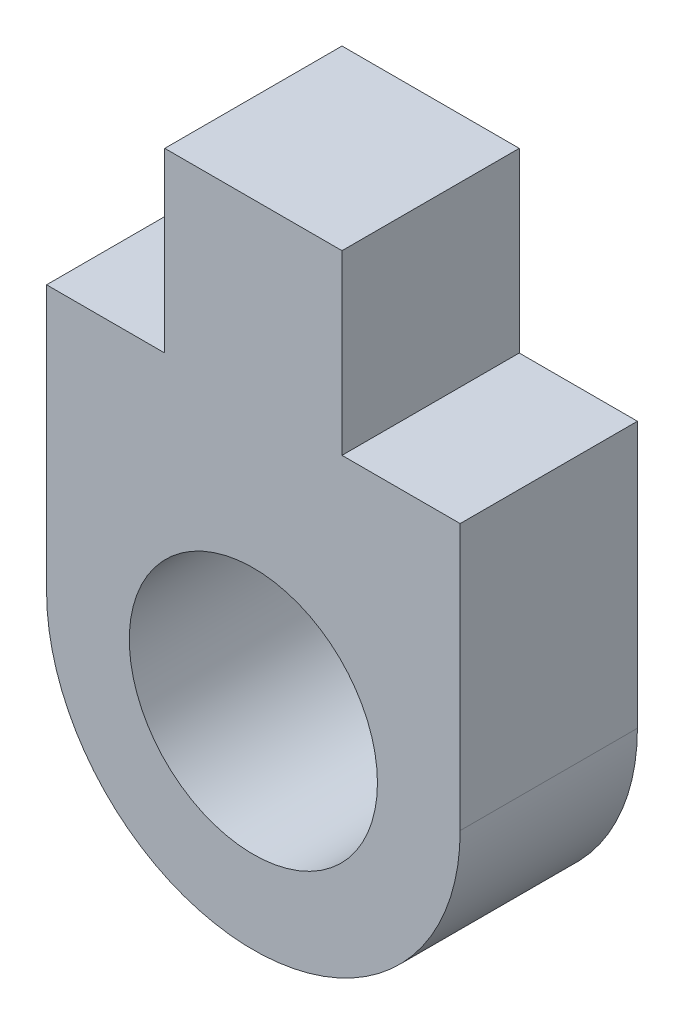
SolidWorks part; units mm, degrees
ref_plane "Alzado" through (0, 0, 0) normal (0, 0, 1) x (1, 0, 0)
ref_plane "Planta" through (0, 0, 0) normal (0, 1, 0) x (1, 0, 0)
ref_plane "Vista lateral" through (0, 0, 0) normal (1, 0, 0) x (0, 0, -1)
sketch "Model" plane through (0, 0, 0) normal (0, 0, 1) x (1, 0, 0)
  line L0 (3.4, -0.3) -> (3.4, 4.2)
  line L1 (1.4, 7.2) -> (-1.6, 7.2)
  line L2 (-3.6, 4.2) -> (-3.6, -0.3)
  line L3 (3.4, 4.2) -> (1.4, 4.2)
  line L4 (-3.6, 4.2) -> (-1.6, 4.2)
  line L5 (1.4, 4.2) -> (1.4, 7.2)
  line L6 (-1.6, 4.2) -> (-1.6, 7.2)
  circle A0 centre (-0.1, -0.3) radius 2.1
  arc A1 (-3.6, -0.3) -> (3.4, -0.3) centre (-0.1, -0.3) ccw
extrude "Saliente-Extruir1" add sketch "Model" along normal blind 3
